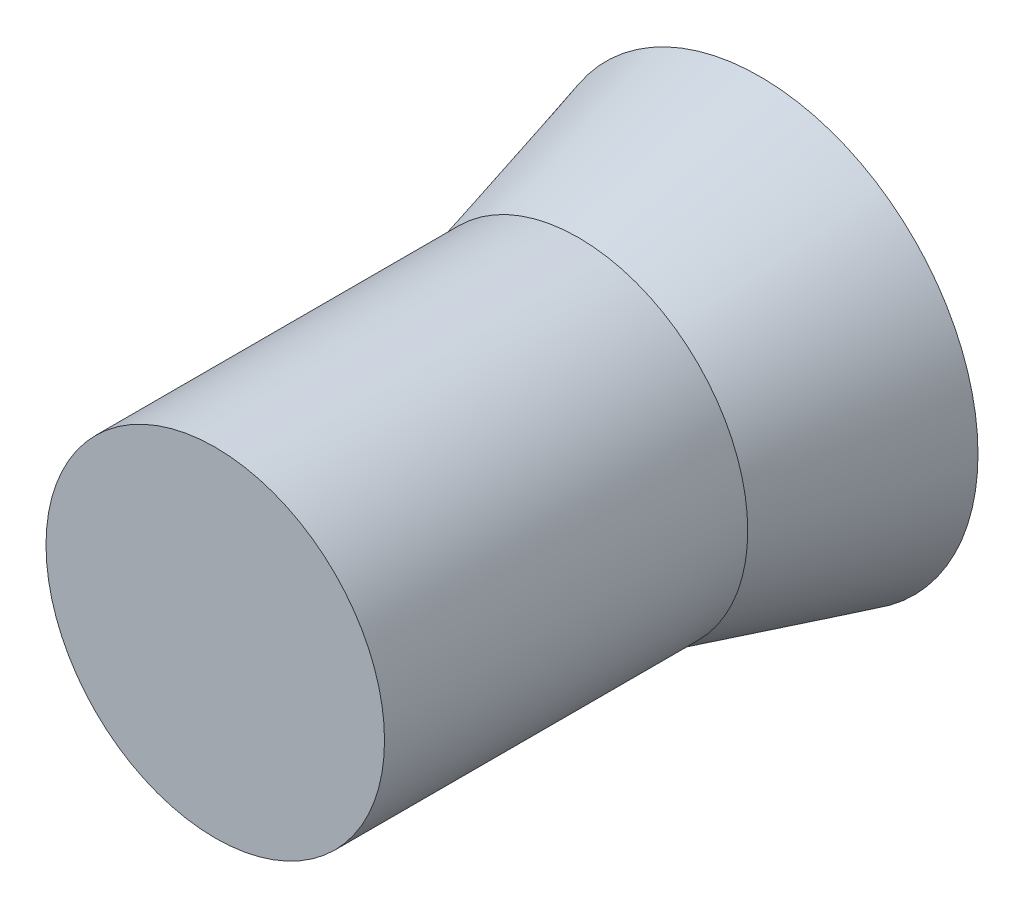
SolidWorks part; units mm, degrees
ref_plane "前基準面" through (0, 0, 0) normal (0, 0, 1) x (1, 0, 0)
ref_plane "上基準面" through (0, 0, 0) normal (0, 1, 0) x (1, 0, 0)
ref_plane "右基準面" through (0, 0, 0) normal (1, 0, 0) x (0, 0, -1)
sketch "草圖1" plane through (0, 0, 0) normal (0, 0, 1) x (1, 0, 0)
  circle A0 centre (0, 0) radius 2.4
  dimension "D1" = 4.8
extrude "填料-伸長1" add sketch "草圖1" along normal blind 2 draft 15
sketch "草圖2" plane through (0, 0, 2) normal (0, 0, 1) x (1, 0, 0)
  circle A1 centre (0, 0) radius 1.8641
  circle A2 centre (0, 0) radius 1.8641
  dimension "D1" = 0
extrude "填料-伸長2" add sketch "草圖2" along normal blind 4
sketch "草圖3" plane through (0, 0, 6) normal (0, 0, 1) x (1, 0, 0)
  circle A0 centre (0, 0) radius 1.55
  dimension "D1" = 3.1
extrude "填料-伸長3" [suppressed] add sketch "草圖3" along normal blind 1.5
sketch "草圖4" [suppressed] plane through (0, 0, 0) normal (0, 1, 0) x (1, 0, 0)
  line L0 (0, -13.5) -> (1.55, -13.5)
  line L1 (-1.55, -13.5) -> (1.55, -13.5) construction
  line L2 (1.55, -13.5) -> (1.65, -13.6732)
  line L3 (1.65, -13.6732) -> (1.65, -14.1732)
  line L4 (1.65, -14.1732) -> (1.55, -14.3464)
  line L5 (1.55, -14.3464) -> (0, -14.3464)
  line L6 (0, -14.3464) -> (0, -13.5) construction
  line L7 (0, -13.5) -> (0, -14.3464)
  dimension "D1" = 0.1
  dimension "D2" = 30
  dimension "D3" = 0.5
  dimension "D4" = 30
revolve "旋轉1" [suppressed] add sketch "草圖4" angle 360 about L6
sketch "草圖5" [suppressed] plane through (0, 0, 14.3464) normal (0, 0, 1) x (1, 0, 0)
  line L0 (-1.8641, 0) -> (1.8641, 0)
  circle A0 centre (0, 0) radius 1.8641 construction
  circle A1 centre (0, 0) radius 1.8641 construction
extrude "除料-伸長-薄件1" [suppressed] cut sketch "草圖5" against normal up to surface and the other way through all thin
fillet "圓角5" [suppressed] radius 0.5
pattern_linear "直線複製排列1" [suppressed] count 3 spacing 5 count 3 spacing 5
